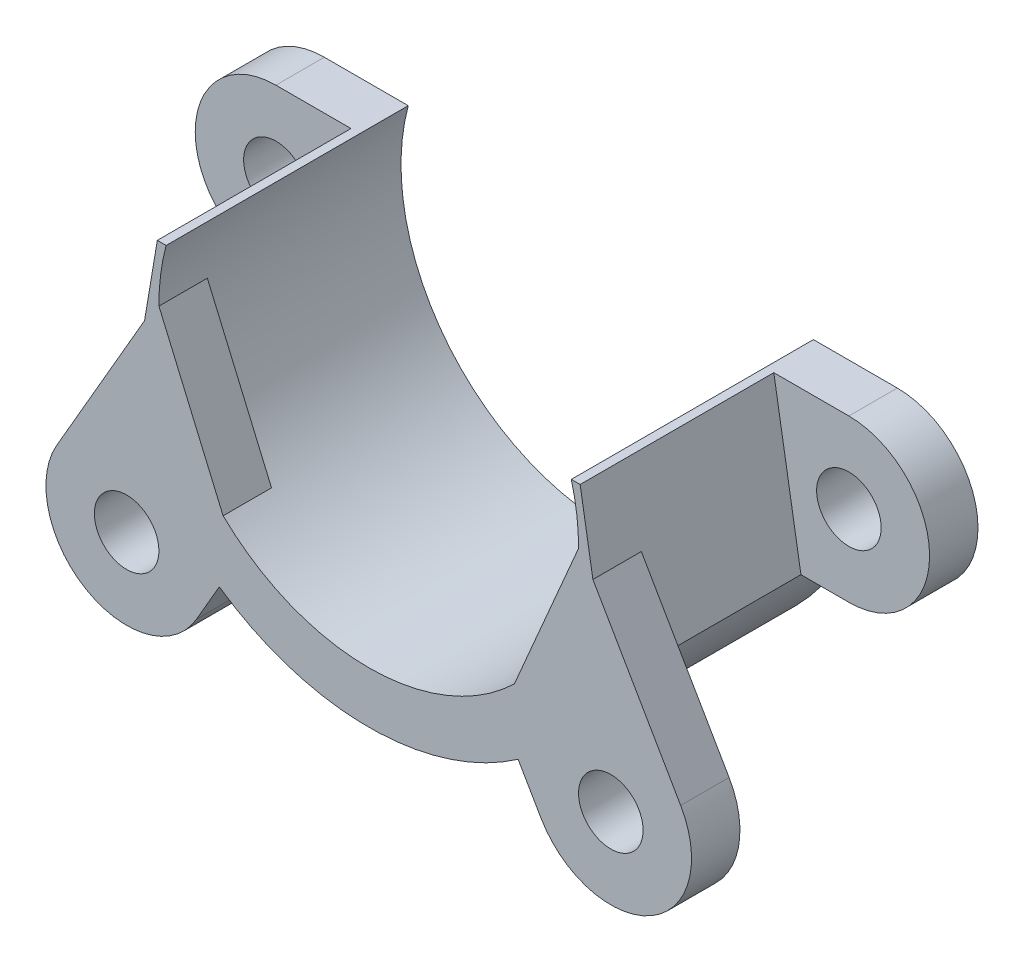
SolidWorks part; units mm, degrees
ref_plane "Plano frontal" through (0, 0, 0) normal (0, 0, 1) x (1, 0, 0)
ref_plane "Plano superior" through (0, 0, 0) normal (0, 1, 0) x (1, 0, 0)
ref_plane "Plano direito" through (0, 0, 0) normal (1, 0, 0) x (0, 0, -1)
sketch "Esboço1" plane through (0, 0, 0) normal (0, 0, 1) x (1, 0, 0)
  line L0 (-17.75, 3.3829) -> (-13.0991, 3.3829)
  line L1 (-17.75, -6.6171) -> (-14.7796, -6.6171)
  line L2 (17.75, 3.3829) -> (13.0991, 3.3829)
  line L3 (14.7796, -6.6171) -> (17.75, -6.6171)
  line L4 (-13.0991, 3.3829) -> (-12.5521, 3.3829)
  line L5 (12.5521, 3.3829) -> (13.0991, 3.3829)
  arc A0 (-12.5521, 3.3829) -> (12.5521, 3.3829) centre (0, 0) ccw
  circle A2 centre (-17.75, -1.6171) radius 2
  circle A3 centre (17.75, -1.6171) radius 2
  arc A4 (-17.75, 3.3829) -> (-17.75, -6.6171) centre (-17.75, -1.6171) ccw
  arc A5 (17.75, -6.6171) -> (17.75, 3.3829) centre (17.75, -1.6171) ccw
  arc A7 (-14.7796, -6.6171) -> (14.7796, -6.6171) centre (0, 0) ccw
  point P8 (0, 0)
  dimension "D1" = 13
  dimension "D4" = 4
  dimension "D3" = 35.5
extrude "Ressalto-extrusão1" add sketch "Esboço1" along normal blind 3
sketch "Esboço2" plane through (0, 0, 3) normal (0, 0, 1) x (1, 0, 0)
  line L1 (13.0991, 3.3829) -> (14.7796, -6.6171)
  line L2 (-14.7796, -6.6171) -> (-13.0991, 3.3829)
  line L8 (-13.0991, 3.3829) -> (-12.5521, 3.3829)
  line L9 (12.5521, 3.3829) -> (13.0991, 3.3829)
  arc A0 (-14.7796, -6.6171) -> (14.7796, -6.6171) centre (0, 0) ccw construction
  arc A2 (-14.7796, -6.6171) -> (14.7796, -6.6171) centre (0, 0) ccw
  arc A4 (-12.5521, 3.3829) -> (12.5521, 3.3829) centre (0, 0) ccw construction
  arc A5 (-12.5521, 3.3829) -> (12.5521, 3.3829) centre (0, 0) ccw
extrude "Ressalto-extrusão2" add sketch "Esboço2" along normal blind 12
sketch "Esboço3" plane through (0, 0, 15) normal (0, 0, 1) x (1, 0, 0)
  line L1 (8.1548, 4.941) -> (8.1548, -16.0857) construction
  line L2 (14.7796, -6.6171) -> (13.0991, 3.3829) construction
  line L3 (13.0772, 0.0835) -> (8.1548, -11.3798)
  line L4 (0, 0) -> (0, 9.938) construction
  line L5 (-8.1548, 4.941) -> (-8.1548, -16.0857) construction
  line L6 (-10.6717, -15.7319) -> (-8.1548, -11.3798)
  line L7 (-19.3283, -10.7256) -> (-13.0772, 0.0835)
  line L8 (-13.0772, 0.0835) -> (-8.1548, -11.3798)
  line L11 (19.3283, -10.7256) -> (13.0772, 0.0835)
  line L16 (10.6717, -15.7319) -> (8.1548, -11.3798)
  arc A1 (-14.7796, -6.6171) -> (14.7796, -6.6171) centre (0, 0) ccw construction
  arc A2 (-10.6717, -15.7319) -> (-19.3283, -10.7256) centre (-15, -13.2288) cw
  circle A3 centre (-15, -13.2288) radius 2
  circle A6 centre (15, -13.2288) radius 2
  arc A7 (10.6717, -15.7319) -> (19.3283, -10.7256) centre (15, -13.2288) ccw
  dimension "D1" = 5
  dimension "D2" = 20
  dimension "D3" = 30
extrude "Ressalto-extrusão3" add sketch "Esboço3" against normal blind 3
